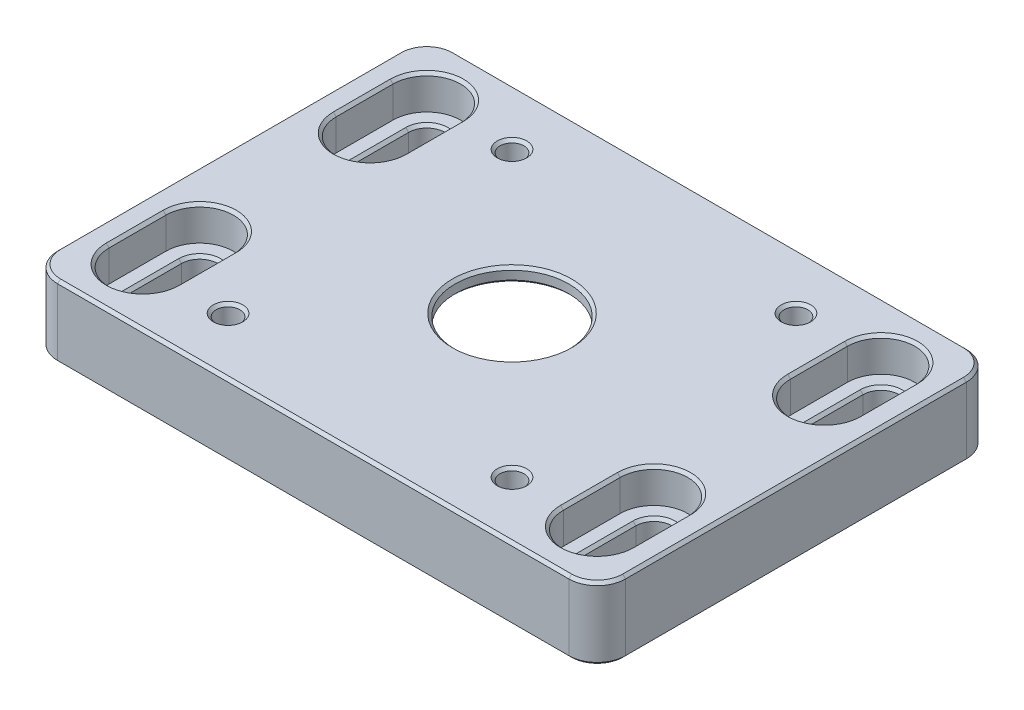
SolidWorks part; units mm, degrees
other "Markup1"
sketch "Sketch8" plane through (-50, 12.7, 35) normal (-0.3262, 0.5647, 0.7581) x (0.9186, 0, 0.3952)
ref_plane "Front Plane" through (0, 0, 0) normal (0, 0, 1) x (1, 0, 0)
ref_plane "Top Plane" through (0, 0, 0) normal (0, 1, 0) x (1, 0, 0)
ref_plane "Right Plane" through (0, 0, 0) normal (1, 0, 0) x (0, 0, -1)
sketch "Sketch1" plane through (0, 0, 0) normal (0, 1, 0) x (1, 0, 0)
  line L1 (50, -35) -> (-50, -35)
  line L2 (50, -35) -> (50, 35)
  line L3 (50, 35) -> (-50, 35)
  line L4 (-50, -35) -> (-50, 35)
  line L5 (50, -35) -> (-50, 35) construction
  line L6 (50, 35) -> (-50, -35) construction
  point P0 (0, 0)
  dimension "D1" = 70
  dimension "D2" = 100
extrude "Boss-Extrude1" add sketch "Sketch1" along normal blind 12.7
sketch "Sketch2" plane through (0, 0, 0) normal (0, -1, 0) x (1, 0, 0)
  circle A0 centre (0, 0) radius 25
  dimension "D1" = 50
extrude "Cut-Extrude1" cut sketch "Sketch2" against normal blind 3
sketch "Sketch3" plane through (0, 3, 0) normal (0, -1, 0) x (1, 0, 0)
  circle A0 centre (0, 0) radius 10
  dimension "D1" = 20
extrude "Cut-Extrude2" cut sketch "Sketch3" against normal through all
sketch "Sketch4" plane through (0, 0, 0) normal (0, -1, 0) x (1, 0, 0)
  line L1 (25, -25) -> (-25, -25) construction
  line L2 (25, -25) -> (25, 25) construction
  line L3 (25, 25) -> (-25, 25) construction
  line L4 (-25, -25) -> (-25, 25) construction
  line L5 (25, -25) -> (-25, 25) construction
  line L6 (25, 25) -> (-25, -25) construction
  circle A0 centre (-25, 25) radius 2.1
  circle A1 centre (25, 25) radius 2.1
  circle A2 centre (25, -25) radius 2.1
  circle A3 centre (-25, -25) radius 2.1
  point P0 (0, 0)
  dimension "D2" = 4.2
  dimension "D1" = 50
extrude "Cut-Extrude3" cut sketch "Sketch4" against normal through all
sketch "Sketch5" plane through (0, 0, 0) normal (0, -1, 0) x (1, 0, 0)
  line L1 (30.25, -30.25) -> (-30.25, -30.25)
  line L2 (30.25, -30.25) -> (30.25, 30.25)
  line L3 (30.25, 30.25) -> (-30.25, 30.25)
  line L4 (-30.25, -30.25) -> (-30.25, 30.25)
  line L5 (30.25, -30.25) -> (-30.25, 30.25) construction
  line L6 (30.25, 30.25) -> (-30.25, -30.25) construction
  point P0 (0, 0)
  dimension "D1" = 60.5
extrude "Cut-Extrude4" cut sketch "Sketch5" against normal blind 7
fillet "Fillet1" radius 3 4 edges at (30.25, 3.5, 30.25) (30.25, 3.5, -30.25) (-30.25, 3.5, -30.25) (-30.25, 3.5, 30.25)
fillet "Fillet2" radius 5 4 edges at (-50, 6.35, -35) (50, 6.35, -35) (-50, 6.35, 35) (50, 6.35, 35)
sketch "Sketch6" plane through (0, 12.7, 0) normal (0, 1, 0) x (1, 0, 0)
  line L0 (-40, 25) -> (-40, 15) construction
  line L1 (40, -25) -> (-40, -25) construction
  line L2 (40, -25) -> (40, 25) construction
  line L3 (40, 25) -> (-40, 25) construction
  line L4 (-40, -25) -> (-40, 25) construction
  line L5 (40, -25) -> (-40, 25) construction
  line L6 (40, 25) -> (-40, -25) construction
  line L9 (0, 0) -> (-40, 0) construction
  line L10 (0, 0) -> (0, 25) construction
  line L11 (-36.8, 25) -> (-36.8, 15)
  line L14 (-43.2, 25) -> (-43.2, 15)
  line L17 (-50, 30) -> (-50, -30) construction
  line L21 (-40, -25) -> (-40, -15) construction
  line L22 (-36.8, -25) -> (-36.8, -15)
  line L23 (-43.2, -25) -> (-43.2, -15)
  line L24 (40, -25) -> (40, -15) construction
  line L25 (36.8, -25) -> (36.8, -15)
  line L26 (43.2, -25) -> (43.2, -15)
  line L27 (40, 25) -> (40, 15) construction
  line L28 (36.8, 25) -> (36.8, 15)
  line L29 (43.2, 25) -> (43.2, 15)
  arc A9 (-36.8, 25) -> (-43.2, 25) centre (-40, 25) ccw
  arc A10 (-43.2, 15) -> (-36.8, 15) centre (-40, 15) ccw
  arc A11 (-36.8, -25) -> (-43.2, -25) centre (-40, -25) cw
  arc A12 (-43.2, -15) -> (-36.8, -15) centre (-40, -15) cw
  arc A13 (36.8, -25) -> (43.2, -25) centre (40, -25) ccw
  arc A14 (43.2, -15) -> (36.8, -15) centre (40, -15) ccw
  arc A15 (36.8, 25) -> (43.2, 25) centre (40, 25) cw
  arc A16 (43.2, 15) -> (36.8, 15) centre (40, 15) cw
  point P0 (0, 0)
  point P6 (-40, 20)
  point P8 (-25, 25)
  point P20 (-40, -20)
  point P26 (40, -20)
  point P32 (40, 20)
  dimension "D2" = 6.4
  dimension "D1" = 10
  dimension "D3" = 10
extrude "Cut-Extrude5" cut sketch "Sketch6" against normal through all
sketch "Sketch7" plane through (0, 7, 0) normal (0, -1, 0) x (1, 0, 0)
  circle A0 centre (0, 0) radius 25.25
  dimension "D1" = 50.5
extrude "Cut-Extrude6" cut sketch "Sketch7" against normal blind 3.2
sketch "Sketch9" plane through (0, 12.7, 0) normal (0, 1, 0) x (1, 0, 0)
  line L7 (45.95, 15) -> (45.95, 25)
  line L8 (34.05, 25) -> (34.05, 15)
  line L9 (45.95, 15) -> (45.95, 25)
  line L10 (34.05, 25) -> (34.05, 15)
  line L32 (0, 0) -> (0, 35) construction
  line L33 (45, 35) -> (-45, 35) construction
  line L34 (34.05, -25) -> (34.05, -15)
  line L35 (45.95, -15) -> (45.95, -25)
  line L38 (0, 0) -> (50, 0) construction
  line L39 (50, -30) -> (50, 30) construction
  line L40 (-45.95, -15) -> (-45.95, -25)
  line L41 (-34.05, -25) -> (-34.05, -15)
  line L42 (-34.05, 25) -> (-34.05, 15)
  line L43 (-45.95, 15) -> (-45.95, 25)
  arc A8 (34.05, 15) -> (45.95, 15) centre (40, 15) ccw
  arc A9 (45.95, 25) -> (34.05, 25) centre (40, 25) ccw
  arc A10 (34.05, 15) -> (45.95, 15) centre (40, 15) ccw
  arc A11 (45.95, 25) -> (34.05, 25) centre (40, 25) ccw
  arc A31 (45.95, -25) -> (34.05, -25) centre (40, -25) cw
  arc A32 (34.05, -15) -> (45.95, -15) centre (40, -15) cw
  arc A33 (-34.05, -15) -> (-45.95, -15) centre (-40, -15) ccw
  arc A34 (-45.95, -25) -> (-34.05, -25) centre (-40, -25) ccw
  arc A37 (-45.95, 25) -> (-34.05, 25) centre (-40, 25) cw
  arc A38 (-34.05, 15) -> (-45.95, 15) centre (-40, 15) cw
  dimension "D2" = 11.9
  dimension "D1" = 2.75
extrude "Cut-Extrude7" cut sketch "Sketch9" against normal blind 6
chamfer "Chamfer1" distance 0.5 angle 45 75 edges at (-36.8, 0, 20) (-40, 0, 11.8) (-40, 0, 28.2) (-43.2, 0, 20) (-36.8, 0, -20) (-40, 0, -28.2) (-40, 0, -11.8) (-43.2, 0, -20) (43.2, 0, 20) (40, 0, 11.8) (40, 0, 28.2) (36.8, 0, 20) (43.2, 0, -20) (40, 0, -28.2) (40, 0, -11.8) (36.8, 0, -20) (0, 0, -35) (-48.5355, 0, -33.5355) (48.5355, 0, -33.5355) (-50, 0, 0) (50, 0, 0) (-48.5355, 0, 33.5355) (48.5355, 0, 33.5355) (0, 0, 35) (0, 12.7, -10) (-40, 12.7, 30.95) (-34.05, 12.7, 20) (-45.95, 12.7, 20) (-40, 12.7, 9.05) (-40, 12.7, -9.05) (-34.05, 12.7, -20) (-45.95, 12.7, -20) (-40, 12.7, -30.95) (-50, 12.7, 0) (-48.5355, 12.7, 33.5355) (-48.5355, 12.7, -33.5355) (0, 12.7, 35) (0, 12.7, -35) (48.5355, 12.7, 33.5355) (48.5355, 12.7, -33.5355) (50, 12.7, 0) (45.95, 12.7, -20) (40, 12.7, -30.95) (40, 12.7, -9.05) (34.05, 12.7, -20) (40, 12.7, 30.95) (45.95, 12.7, 20) (34.05, 12.7, 20) (40, 12.7, 9.05) (0, 7, -25.25) (0, 10.2, -10) (-40, 6.7, 28.2) (-43.2, 6.7, 20) (-36.8, 6.7, 20) (-40, 6.7, 11.8) (-40, 6.7, -11.8) (-36.8, 6.7, -20) (-43.2, 6.7, -20) (-40, 6.7, -28.2) (40, 6.7, -11.8) (36.8, 6.7, -20) (43.2, 6.7, -20) (40, 6.7, -28.2) (40, 6.7, 28.2) (43.2, 6.7, 20) (36.8, 6.7, 20) (40, 6.7, 11.8) (-25, 7, 22.9) (-25, 12.7, 22.9) (-25, 7, -27.1) (-25, 12.7, -27.1) (25, 7, -27.1) (25, 12.7, -27.1) (25, 7, 22.9) (25, 12.7, 22.9)
